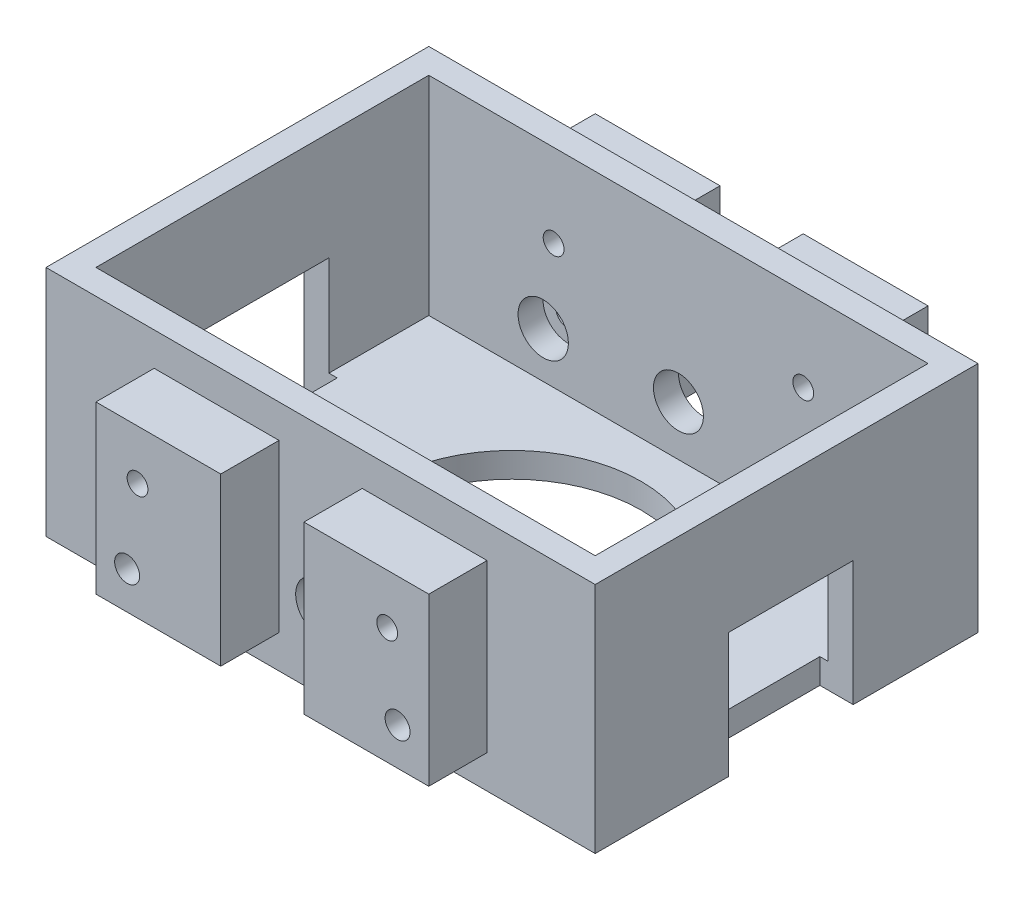
SolidWorks part; units mm, degrees
ref_plane "Front Plane" through (0, 0, 0) normal (0, 0, 1) x (1, 0, 0)
ref_plane "Top Plane" through (0, 0, 0) normal (0, 1, 0) x (1, 0, 0)
ref_plane "Right Plane" through (0, 0, 0) normal (1, 0, 0) x (0, 0, -1)
sketch "Sketch1" plane through (0, 0, 0) normal (0, 1, 0) x (1, 0, 0)
  line L1 (-41.3246, 5.1822) -> (24.6754, 5.1822)
  line L2 (-41.3246, 5.1822) -> (-41.3246, -40.8178)
  line L3 (-41.3246, -40.8178) -> (24.6754, -40.8178)
  line L4 (24.6754, 5.1822) -> (24.6754, -40.8178)
  dimension "D1" = 66
  dimension "D2" = 46
extrude "Boss-Extrude2" add sketch "Sketch1" along normal blind 3
sketch "Sketch3" plane through (0, 3, 0) normal (0, 1, 0) x (1, 0, 0)
  line L0 (-41.3246, 5.1822) -> (-41.3246, -40.8178) construction
  line L1 (-41.3246, 5.1822) -> (-38.3246, 5.1822)
  line L2 (-41.3246, 5.1822) -> (-41.3246, -40.8178)
  line L3 (-41.3246, -40.8178) -> (-38.3246, -40.8178)
  line L4 (-38.3246, 5.1822) -> (-38.3246, -40.8178)
  line L5 (-38.3246, 5.1822) -> (21.6754, 5.1822)
  line L6 (-38.3246, 5.1822) -> (-38.3246, 2.1822)
  line L7 (-38.3246, 2.1822) -> (21.6754, 2.1822)
  line L8 (21.6754, 5.1822) -> (21.6754, 2.1822)
  line L9 (21.6754, 5.1822) -> (24.6754, 5.1822)
  line L10 (21.6754, 5.1822) -> (21.6754, -40.8178)
  line L11 (21.6754, -40.8178) -> (24.6754, -40.8178)
  line L12 (24.6754, 5.1822) -> (24.6754, -40.8178)
  line L13 (-38.3246, -37.8178) -> (21.6754, -37.8178)
  line L14 (-38.3246, -37.8178) -> (-38.3246, -40.8178)
  line L15 (-38.3246, -40.8178) -> (21.6754, -40.8178)
  line L16 (21.6754, -37.8178) -> (21.6754, -40.8178)
  line L17 (24.6754, 5.1822) -> (-41.3246, 5.1822) construction
  line L18 (-41.3246, -40.8178) -> (24.6754, -40.8178) construction
  line L19 (24.6754, -40.8178) -> (24.6754, 5.1822) construction
  point P22 (23.1754, -40.8178)
  dimension "D1" = 3
  dimension "D2" = 3
  dimension "D3" = 3
  dimension "D4" = 3
  dimension "D5" = 0
  dimension "D6" = 0
  dimension "D7" = 0
  dimension "D8" = 0
  dimension "D9" = 0
  dimension "D10" = 0
  dimension "D11" = 0
  dimension "D12" = 0
  dimension "D13" = 0
  dimension "D14" = 0
  dimension "D15" = 0
  dimension "D16" = 0
extrude "Boss-Extrude4" add sketch "Sketch3" along normal blind 25 contours L8 L19 L4 L7 | L4 L19 L0 L17 | L13 L16 L15 L14 | L12 L11 L10 L9
sketch "Sketch4" plane through (0, 0, 40.8178) normal (0, 0, 1) x (1, 0, 0)
  line L0 (24.6754, 28) -> (24.6754, 0) construction
  line L1 (-13.3246, 24) -> (-28.3246, 24)
  line L2 (-13.3246, 24) -> (-13.3246, 4)
  line L3 (-13.3246, 4) -> (-28.3246, 4)
  line L4 (-28.3246, 24) -> (-28.3246, 4)
  line L5 (-3.3246, 24) -> (11.6754, 24)
  line L6 (-3.3246, 24) -> (-3.3246, 4)
  line L7 (-3.3246, 4) -> (11.6754, 4)
  line L8 (11.6754, 24) -> (11.6754, 4)
  line L10 (-41.3246, 0) -> (24.6754, 0) construction
  line L11 (-41.3246, 28) -> (24.6754, 28) construction
  dimension "D1" = 15
  dimension "D2" = 20
  dimension "D3" = 15
  dimension "D4" = 20
  dimension "D5" = 10
  dimension "D6" = 13
  dimension "D7" = 4
  dimension "D8" = 4
extrude "Boss-Extrude5" add sketch "Sketch4" along normal blind 7 contours L8 L5 L6 L7 | L2 L1 L4 L3
sketch "Sketch5" plane through (0, 0, 47.8178) normal (0, 0, 1) x (1, 0, 0)
  line L0 (-41.3246, 28) -> (-41.3246, 0) construction
  line L1 (-41.3246, 28) -> (24.6754, 28) construction
  line L3 (24.6754, 28) -> (24.6754, 0) construction
  circle A2 centre (-24.5746, 8.5) radius 1.5
  circle A3 centre (7.9254, 8.5) radius 1.5
  circle A4 centre (6.6754, 18) radius 1.25
  circle A5 centre (-23.3246, 18) radius 1.25
  dimension "D5" = 16.75
  dimension "D9" = 3
  dimension "D10" = 2.5
  dimension "D11" = 3
  dimension "D12" = 2.5
  dimension "D1" = 32.5
  dimension "D2" = 30
  dimension "D3" = 9.5
  dimension "D4" = 9.5
  dimension "D6" = 10
  dimension "D7" = 16.75
  dimension "D8" = 18
extrude "Cut-Extrude1" cut sketch "Sketch5" against normal up to next
sketch "Sketch6" plane through (0, 0, -5.1822) normal (0, 0, -1) x (-1, 0, 0)
  line L0 (3.3246, 24) -> (-11.6754, 24)
  line L5 (3.3246, 24) -> (3.3246, 4)
  line L6 (3.3246, 4) -> (-11.6754, 4)
  line L7 (-11.6754, 24) -> (-11.6754, 4)
  line L8 (13.3246, 24) -> (28.3246, 24)
  line L9 (13.3246, 24) -> (13.3246, 4)
  line L10 (13.3246, 4) -> (28.3246, 4)
  line L11 (28.3246, 24) -> (28.3246, 4)
  line L13 (-24.6754, 28) -> (41.3246, 28) construction
  line L14 (41.3246, 28) -> (41.3246, 0) construction
  dimension "D1" = 20
  dimension "D2" = 15
  dimension "D3" = 15
  dimension "D4" = 20
  dimension "D5" = 10
  dimension "D6" = 4
  dimension "D7" = 13
  dimension "D8" = 4
extrude "Boss-Extrude6" add sketch "Sketch6" along normal blind 7 contours L0 L7 L6 L5 | L8 L11 L10 L9
sketch "Sketch7" plane through (0, 0, -12.1822) normal (0, 0, -1) x (-1, 0, 0)
  line L1 (-24.6754, 28) -> (-24.6754, 0) construction
  line L3 (-24.6754, 28) -> (41.3246, 28) construction
  circle A1 centre (-7.9254, 8.5) radius 1.5
  circle A2 centre (24.5746, 8.5) radius 1.5
  circle A3 centre (23.3246, 18) radius 1.25
  circle A4 centre (-6.6754, 18) radius 1.25
  dimension "D5" = 2.5
  dimension "D6" = 3
  dimension "D7" = 2.5
  dimension "D8" = 3
  dimension "D9" = 16.75
  dimension "D10" = 10
  dimension "D11" = 18
  dimension "D12" = 10
  dimension "D1" = 32.5
  dimension "D2" = 9.5
  dimension "D3" = 9.5
  dimension "D4" = 30
extrude "Cut-Extrude2" cut sketch "Sketch7" against normal blind 10
sketch "Sketch8" plane through (0, 0, 0) normal (0, -1, 0) x (-1, 0, 0)
  line L0 (-24.6754, 5.1822) -> (41.3246, 5.1822) construction
  line L1 (41.3246, 5.1822) -> (41.3246, -40.8178) construction
  circle A0 centre (8.3246, -17.8178) radius 15.5
  dimension "D1" = 31
  dimension "D2" = 23
  dimension "D3" = 33
extrude "Cut-Extrude3" cut sketch "Sketch8" against normal up to next contours A0
sketch "Sketch11" plane through (0, 0, 40.8178) normal (0, 0, 1) x (1, 0, 0)
  line L0 (24.6754, 28) -> (24.6754, 0) construction
  line L1 (-41.3246, 0) -> (24.6754, 0) construction
  circle A0 centre (-8.3246, 9) radius 3
  dimension "D1" = 6
  dimension "D2" = 33
  dimension "D3" = 9
extrude "Cut-Extrude6" cut sketch "Sketch11" against normal through all and the other way through all
sketch "Sketch12" plane through (0, 0, 37.8178) normal (0, 0, -1) x (-1, 0, 0)
  circle A0 centre (24.5746, 8.5) radius 3.025
  circle A1 centre (24.5746, 8.5) radius 1.5 construction
  circle A2 centre (-7.9254, 8.5) radius 3.025
  circle A5 centre (-7.9254, 8.5) radius 1.5 construction
  dimension "D1" = 6.05
  dimension "D2" = 6.05
extrude "Cut-Extrude7" cut sketch "Sketch12" against normal blind 3
sketch "Sketch14" plane through (0, 0, -2.1822) normal (0, 0, 1) x (1, 0, 0)
  circle A0 centre (-24.5746, 8.5) radius 3.025
  circle A1 centre (-24.5746, 8.5) radius 1.5 construction
  circle A2 centre (7.9254, 8.5) radius 3.025
  circle A3 centre (7.9254, 8.5) radius 1.5 construction
  dimension "D1" = 6.05
  dimension "D2" = 6.05
extrude "Cut-Extrude8" cut sketch "Sketch14" against normal blind 3
sketch "Sketch15" plane through (0, 0, 0) normal (0, -1, 0) x (-1, 0, 0)
  line L0 (-24.6754, -40.8178) -> (-24.6754, 5.1822) construction
  line L1 (-24.6754, -9.8178) -> (-20.6754, -9.8178)
  line L2 (-24.6754, -9.8178) -> (-24.6754, -24.8178)
  line L3 (-24.6754, -24.8178) -> (-20.6754, -24.8178)
  line L4 (-20.6754, -9.8178) -> (-20.6754, -24.8178)
  line L5 (-24.6754, 5.1822) -> (41.3246, 5.1822) construction
  line L7 (37.3246, -9.8178) -> (41.3246, -9.8178)
  line L8 (37.3246, -9.8178) -> (37.3246, -24.8178)
  line L9 (37.3246, -24.8178) -> (41.3246, -24.8178)
  line L10 (41.3246, -9.8178) -> (41.3246, -24.8178)
  line L11 (41.3246, 5.1822) -> (41.3246, -40.8178) construction
  line M12 (-24.6754, 5.1822) -> (-24.6754, -40.8178)
  dimension "D1" = 15
  dimension "D2" = 4
  dimension "D3" = 15
  dimension "D4" = 0
  dimension "D5" = 15
  dimension "D6" = 4
  dimension "D7" = 15
extrude "Cut-Extrude10" cut sketch "Sketch15" against normal blind 15 contours L4 L1 L3 M12 | L7 L10 L9 L8
